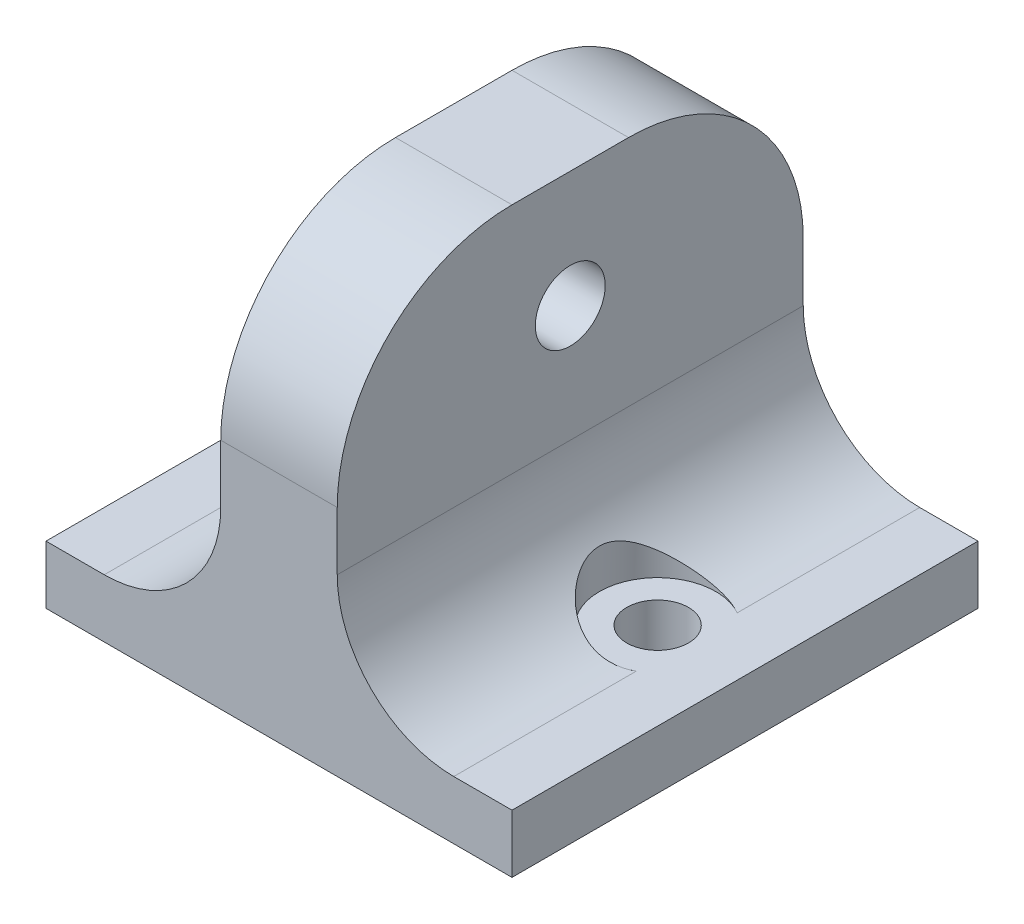
SolidWorks part; units mm, degrees
material "ABS"
ref_plane "Front Plane" through (0, 0, 0) normal (0, 0, 1) x (1, 0, 0)
ref_plane "Top Plane" through (0, 0, 0) normal (0, 1, 0) x (1, 0, 0)
ref_plane "Right Plane" through (0, 0, 0) normal (1, 0, 0) x (0, 0, -1)
sketch "Sketch1" plane through (0, 0, 0) normal (0, 1, 0) x (1, 0, 0)
  line L5 (-10, 10) -> (10, -10) construction
  line L6 (-10, -10) -> (10, 10) construction
  line L7 (-20, 20) -> (20, 20)
  line L8 (-20, 20) -> (-20, -20)
  line L9 (-20, -20) -> (20, -20)
  line L10 (20, 20) -> (20, -20)
  line L11 (-20, 20) -> (20, -20) construction
  line L12 (-20, -20) -> (20, 20) construction
  point P0 (0, 0)
  point P6 (0, 0)
  dimension "D3" = 40
  dimension "D4" = 40
extrude "Boss-Extrude1" add sketch "Sketch1" along normal blind 5
sketch "Sketch4" plane through (0, 5, 0) normal (0, 1, 0) x (1, 0, 0)
  line L1 (-5, -20) -> (5, -20)
  line L2 (-5, -20) -> (-5, 20)
  line L3 (-5, 20) -> (5, 20)
  line L4 (5, -20) -> (5, 20)
  line L5 (-5, -20) -> (5, 20) construction
  line L6 (-5, 20) -> (5, -20) construction
  line L7 (-20, 20) -> (20, 20) construction
  point P0 (0, 0)
  dimension "D1" = 10
extrude "Boss-Extrude3" add sketch "Sketch4" along normal blind 30
sketch "Sketch5" plane through (5, 0, 0) normal (1, 0, 0) x (0, 0, -1)
  line L0 (20, 5) -> (-20, 5) construction
  circle A0 centre (0, 25) radius 3
  dimension "D1" = 6
  dimension "D2" = 20
extrude "Cut-Extrude4" cut sketch "Sketch5" against normal through all
fillet "Fillet1" radius 15 2 edges at (0, 35, -20) (0, 35, 20)
fillet "Filete1" radius 10 2 edges at (5, 5, 0) (-5, 5, 0)
sketch "Esboço1" plane through (0, 5, 0) normal (0, 1, 0) x (1, 0, 0)
  line L0 (-5, 20) -> (-5, 5) construction
  line L3 (5, -20) -> (5, -5) construction
  circle A0 centre (-12.5, 0) radius 2.65
  circle A1 centre (12.5, 0) radius 2.65
  dimension "D1" = 5.3
  dimension "D2" = 5.3
  dimension "D3" = 7.5
  dimension "D4" = 7.5
extrude "Corte-extrusão1" cut sketch "Esboço1" against normal through all both and the other way through all
sketch "Esboço2" plane through (0, 5, 0) normal (0, 1, 0) x (1, 0, 0)
  circle A0 centre (-12.5, 0) radius 5
  circle A1 centre (12.5, 0) radius 5
  dimension "D1" = 10
  dimension "D2" = 10
extrude "Corte-extrusão2" cut sketch "Esboço2" along normal through all
equation "\"D2@Esboço1\"=\"D1@Esboço1\""
equation "\"D2@Esboço2\"=\"D1@Esboço2\""
